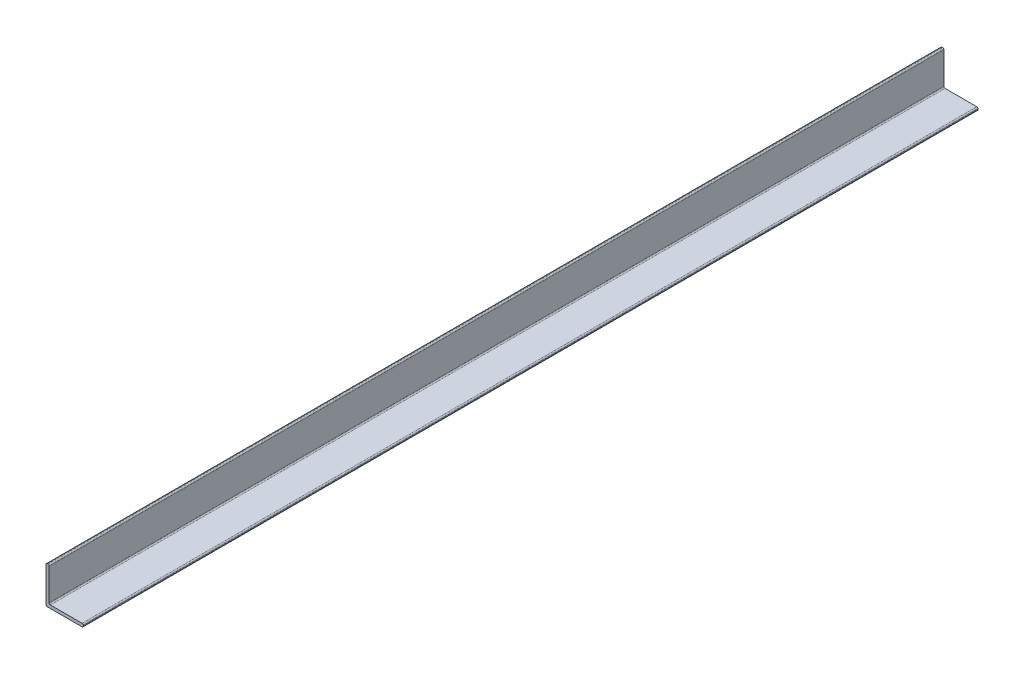
SolidWorks part; units mm, degrees
material "1023 Carbon Steel Sheet (SS)"
ref_plane "Front Plane" through (0, 0, 0) normal (0, 0, 1) x (1, 0, 0)
ref_plane "Top Plane" through (0, 0, 0) normal (0, 1, 0) x (1, 0, 0)
ref_plane "Right Plane" through (0, 0, 0) normal (1, 0, 0) x (0, 0, -1)
sketch "Sketch1" plane through (0, 0, 0) normal (0, 0, 1) x (1, 0, 0)
  line L0 (0, -38.1) -> (0, 38.1) construction
  line L1 (38.1, 0) -> (-38.1, 0) construction
  line L2 (-38.1, 38.1) -> (-38.1, -38.1) construction
  line L3 (-38.1, -38.1) -> (38.1, -38.1) construction
  line L4 (38.1, -38.1) -> (38.1, -31.75) construction
  line L5 (38.1, -31.75) -> (-31.75, -31.75) construction
  line L6 (-31.75, -31.75) -> (-31.75, 38.1) construction
  line L7 (-31.75, 38.1) -> (-38.1, 38.1) construction
  line L8 (-31.75, -31.75) -> (-38.1, -31.75) construction
  line L9 (-31.75, -31.75) -> (-31.75, -38.1) construction
  point P4 (0, 0)
  point P8 (0, 0)
  point P14 (38.1, -31.877)
  dimension "Wall Thickness" = 6.35
  dimension "Outside Height" = 76.2
  dimension "Outside Width" = 76.2
  dimension "Inside Width" = 69.85
  dimension "Inside Height" = 69.85
  dimension "Finish Thickness" = 0.254
sketch "Sketch2" plane through (0, 0, 0) normal (1, 0, 0) x (0, 0, -1)
  line L0 (914.4, 0) -> (-914.4, 0) construction
  line L1 (914.4, -38.1) -> (-914.4, -38.1) construction
  point P0 (-819.15, 0)
  point P4 (0, 0)
  point P5 (819.15, 0)
  point P9 (0, -38.1)
  dimension "Length" = 1828.8
  dimension "D1" = 95.25
  dimension "D2" = 95.25
sketch "Sketch4" plane through (0, 0, 0) normal (0, 0, 1) x (1, 0, 0)
  line L0 (-31.75, -31.75) -> (-31.75, 38.1) construction
  line L1 (38.1, -31.75) -> (-31.75, -31.75) construction
  line L2 (38.1, -38.1) -> (38.1, -31.75) construction
  line L3 (-38.1, -38.1) -> (38.1, -38.1) construction
  line L4 (-38.1, 38.1) -> (-38.1, -38.1) construction
  line L5 (-31.75, 38.1) -> (-38.1, 38.1) construction
  line L6 (-31.75, -29.21) -> (-31.75, 38.1)
  line L7 (38.1, -31.75) -> (-29.21, -31.75)
  line L8 (38.1, -38.1) -> (38.1, -31.75)
  line L9 (-38.1, -38.1) -> (38.1, -38.1)
  line L10 (-38.1, 38.1) -> (-38.1, -38.1)
  line L11 (-31.75, 38.1) -> (-38.1, 38.1)
  arc A0 (-31.75, -29.21) -> (-29.21, -31.75) centre (-29.21, -29.21) ccw
extrude "Boss-Extrude1" add sketch "Sketch4" against normal up to vertex (914.4 mm away) and the other way up to vertex (914.4 mm away) up to point (0, 0, -914.4) other way up to point (0, 0, 914.4)
fillet "Fillet1" radius 2.54 5 edges at (-38.1, -38.1, 0) (38.1, -38.1, 0) (38.1, -31.75, 0) (-38.1, 38.1, 0) (-31.75, 38.1, 0)
equation "\"D1@Sketch2\"=\"Outside Height@Sketch1\"*1.25"
equation "\"D2@Sketch2\"=\"D1@Sketch2\""
equation "\"D1@Sketch4\"=\"Wall Thickness@Sketch1\"/2.5"
equation "\"D1@Fillet1\"=\"D1@Sketch4\""
